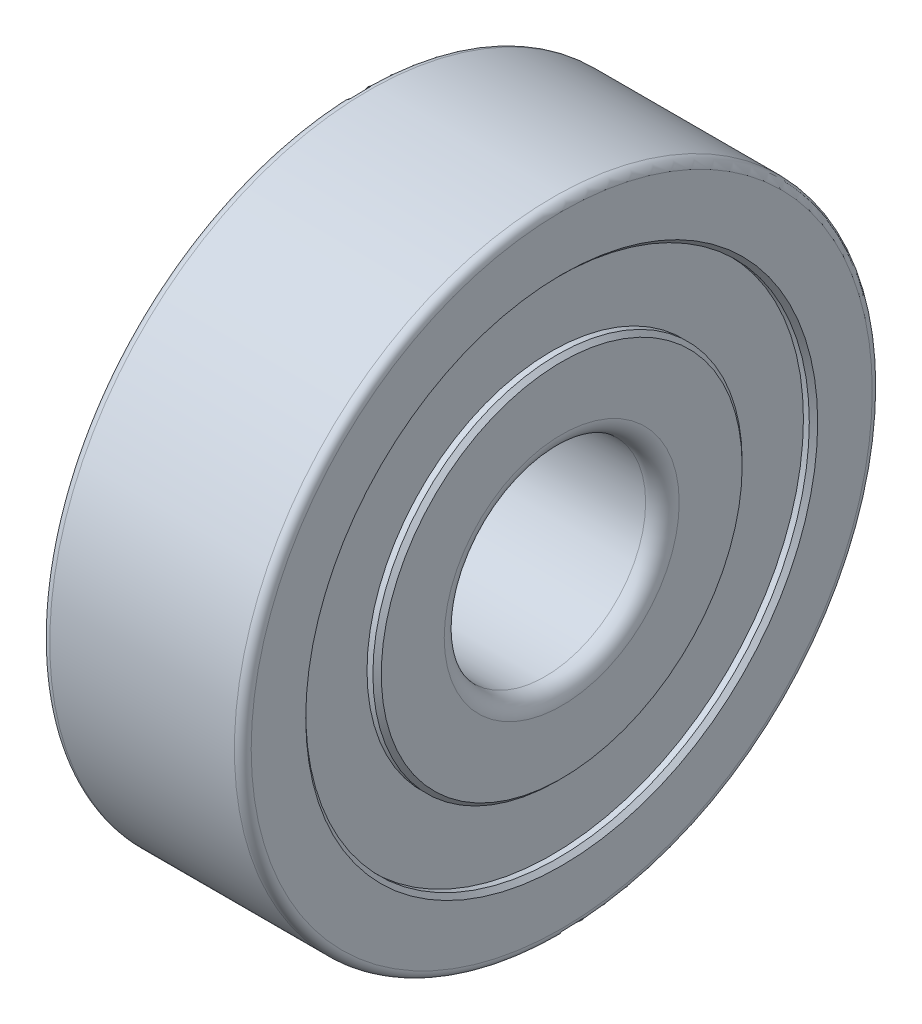
SolidWorks part; units mm, degrees
ref_plane "Front Plane" through (0, 0, 0) normal (0, 0, 1) x (1, 0, 0)
ref_plane "Top Plane" through (0, 0, 0) normal (0, 1, 0) x (1, 0, 0)
ref_plane "Right Plane" through (0, 0, 0) normal (1, 0, 0) x (0, 0, -1)
sketch "Sketch1" plane through (0, 0, 0) normal (0, 0, 1) x (1, 0, 0)
  line L0 (0, 0) -> (-6, 0) construction
  line L1 (-5.875, 5.5) -> (-4.299, 5.5)
  line L2 (-0.5, 3) -> (-5.5, 3)
  line L3 (0, 3.5) -> (0, 5.375)
  line L4 (-0.25, 9.5) -> (-5.75, 9.5)
  line L5 (-6, 7.625) -> (-6, 9.25)
  line L6 (-5.875, 7.5) -> (-3.8292, 7.5)
  line L7 (0, 7.625) -> (0, 9.25)
  line L8 (-6, 3.5) -> (-6, 5.375)
  line L9 (-1.701, 5.5) -> (-0.125, 5.5)
  line L10 (-2.1708, 7.5) -> (-0.125, 7.5)
  line L11 (-5.875, 7.5) -> (-6, 7.625)
  line L12 (-0.125, 7.5) -> (0, 7.625)
  line L13 (-0.125, 5.5) -> (0, 5.375)
  line L14 (-6, 5.375) -> (-5.875, 5.5)
  arc A0 (-4.299, 5.5) -> (-1.701, 5.5) centre (-3, 6.25) ccw
  arc A1 (-2.1708, 7.5) -> (-3.8292, 7.5) centre (-3, 6.25) ccw
  arc A2 (-5.75, 9.5) -> (-6, 9.25) centre (-5.75, 9.25) ccw
  arc A3 (0, 9.25) -> (-0.25, 9.5) centre (-0.25, 9.25) ccw
  arc A4 (-5.5, 3) -> (-6, 3.5) centre (-5.5, 3.5) cw
  arc A5 (0, 3.5) -> (-0.5, 3) centre (-0.5, 3.5) cw
  point P10 (-6, 5.5)
  point P13 (0, 5.5)
  point P14 (-6, 7.5)
  point P15 (0, 7.5)
  point P18 (-6, 9.5)
  point P23 (-6, 3)
  point P26 (0, 3)
  dimension "D3" = 3
  dimension "D9" = 0.25
  dimension "D10" = 0.5
  dimension "D1" = 6
  dimension "D2" = 3
  dimension "D4" = 6.5
  dimension "D5" = 3
  dimension "D6" = 6.25
  dimension "D7" = 2.5
  dimension "D8" = 2
revolve "Revolve1" add sketch "Sketch1" angle 360 about L0
sketch "Sketch2" plane through (0, 0, 0) normal (0, 0, 1) x (1, 0, 0)
  line L0 (-3, 7.75) -> (-3, 4.75)
  arc A0 (-3, 4.75) -> (-3, 7.75) centre (-3, 6.25) ccw
  dimension "D1" = 3
  dimension "D2" = 6.25
  dimension "D3" = 3
revolve "Revolve2" add sketch "Sketch2" angle 360 about L0
pattern_circular "CirPattern2" count 8 over 360 about axis through (0, 0, 0) along (1, 0, 0) of bodies 109
ref_plane "Plane1" through (-0.5, 0, 0) normal (1, 0, 0) x (0, 0, -1)
sketch "Sketch7" plane through (-0.5, 0, 0) normal (1, 0, 0) x (0, 0, -1)
  circle A0 centre (0, 0) radius 5.5
  circle A1 centre (0, 0) radius 7.5
  dimension "D1" = 15
  dimension "D2" = 11
extrude "Seal 1" add sketch "Sketch7" along normal blind 0.2
ref_plane "Plane2" through (-5.5, 0, 0) normal (-1, 0, 0) x (0, 0, 1)
sketch "Sketch8" plane through (-5.5, 0, 0) normal (-1, 0, 0) x (0, 0, 1)
  circle A0 centre (0, 0) radius 5.5
  circle A1 centre (0, 0) radius 7.5
  dimension "D1" = 15
  dimension "D2" = 11
extrude "Seal 2" add sketch "Sketch8" along normal blind 0.2
